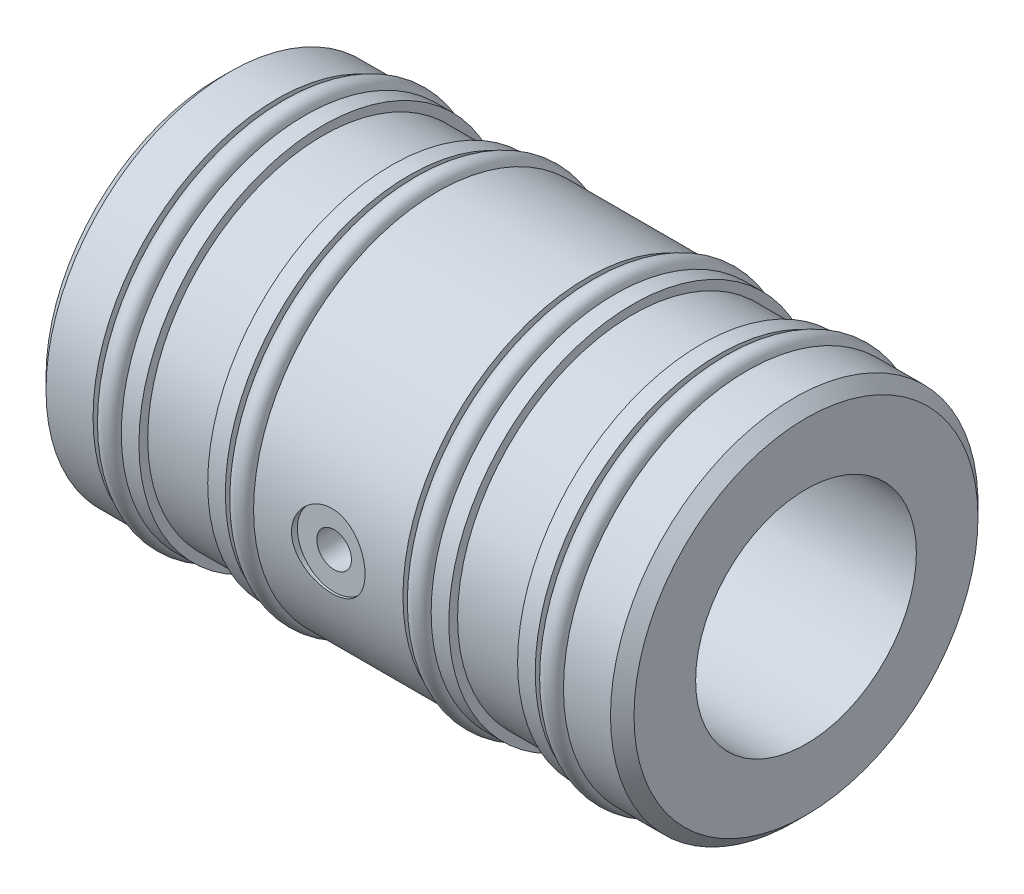
SolidWorks part; units mm, degrees
ref_plane "Front Plane" through (0, 0, 0) normal (0, 0, 1) x (1, 0, 0)
ref_plane "Top Plane" through (0, 0, 0) normal (0, 1, 0) x (1, 0, 0)
ref_plane "Right Plane" through (0, 0, 0) normal (1, 0, 0) x (0, 0, -1)
sketch "Sketch1" plane through (0, 0, 0) normal (0, 0, 1) x (1, 0, 0)
  line L0 (0, 9.5352) -> (50.8, 9.5352)
  line L1 (50.8, 9.5352) -> (50.8, 15.875)
  line L2 (50.8, 15.875) -> (45.72, 15.875)
  line L3 (45.72, 15.875) -> (45.72, 14.605)
  line L4 (45.72, 14.605) -> (43.2816, 14.605)
  line L5 (43.2816, 14.605) -> (43.2816, 15.875)
  line L6 (43.2816, 15.875) -> (41.7576, 15.875)
  line L7 (41.7576, 15.875) -> (41.7576, 15.113)
  line L8 (0, 9.5352) -> (0, 15.875)
  line L9 (0, 15.875) -> (5.08, 15.875)
  line L10 (5.08, 15.875) -> (5.08, 14.605)
  line L11 (5.08, 14.605) -> (7.5184, 14.605)
  line L12 (7.5184, 14.605) -> (7.5184, 15.875)
  line L13 (7.5184, 15.875) -> (9.0424, 15.875)
  line L14 (9.0424, 15.875) -> (9.0424, 15.113)
  line L15 (9.0424, 15.113) -> (14.986, 15.113)
  line L16 (14.986, 15.113) -> (14.986, 15.875)
  line L17 (14.986, 15.875) -> (16.51, 15.875)
  line L18 (16.51, 15.875) -> (16.51, 14.605)
  line L19 (16.51, 14.605) -> (18.9484, 14.605)
  line L20 (18.9484, 14.605) -> (18.9484, 15.875)
  line L21 (18.9484, 15.875) -> (31.8516, 15.875)
  line L22 (31.8516, 15.875) -> (31.8516, 14.605)
  line L23 (41.7576, 15.113) -> (35.814, 15.113)
  line L24 (35.814, 15.113) -> (35.814, 15.875)
  line L25 (35.814, 15.875) -> (34.29, 15.875)
  line L26 (34.29, 15.875) -> (34.29, 14.605)
  line L27 (34.29, 14.605) -> (31.8516, 14.605)
  line L28 (0, 0) -> (50.8, 0) construction
  dimension "Bore ID" = 19.0703
  dimension "OAL" = 50.8
  dimension "Moglice groove width" = 5.9436
  dimension "O-ring groove width" = 2.4384
  dimension "Edge to 1st o-ring groove" = 5.08
  dimension "Edge to 2nd o-ring groove" = 16.51
  dimension "Bushing OD" = 31.75
  dimension "O-ring groove dia" = 29.21
  dimension "Edge to 3rd o-ring groove" = 31.8516
  dimension "edge to 4th o-ring groove" = 43.2816
  dimension "Edge to 1st moglice groove" = 9.0424
  dimension "Edge to 2nd moglice groove" = 35.814
  dimension "Moglice Groove Dia" = 30.226
revolve "Revolve1" add sketch "Sketch1" angle 360 about L28
chamfer "Chamfer1" distance 1.016 angle 45 2 edges at (0, 0, 15.875) (50.8, 0, 15.875)
ref_plane "Plane1" through (0, 0, -7.9121) normal (0, 0, 1) x (1, 0, 0)
hole_wizard "1/4 (0.25) Diameter Hole1" positions "3DSketch1" profile "Sketch2" hole size "1/4" standard "Ansi Inch"
sketch3d "3DSketch1"
  point P0 (25.4, 0, 15.875)
  dimension "Edge to air hole" = 25.4
sketch "Sketch2" plane through (25.4, 0, 15.875) normal (1, 0, 0) x (0, -1, 0)
  line L0 (0, 0) -> (0, 0.508)
  line L1 (0, 0.508) -> (3.175, 0.508)
  line L2 (3.175, 0.508) -> (3.175, 0)
  line L5 (3.175, 0) -> (0, 0)
  line L10 (0, 0.508) -> (-3.175, 0.508) construction
  line L11 (0, -6.35) -> (0, 107.95) construction
  dimension "Hole Dia." = 6.35
  dimension "Hole Depth" = 0.508
  dimension "Drill Angle" = 180
hole_wizard "Air Hole" positions "Sketch4" profile "Sketch3" tap size "M3x0.5" standard "Ansi Metric"
sketch "Sketch4" plane through (0, 0, 15.367) normal (0, 0, 1) x (1, 0, 0)
  circle A0 centre (25.4, 0) radius 3.175 construction
  point P0 (25.4, 0)
sketch "Sketch3" plane through (25.4, 0, 15.367) normal (1, 0, 0) x (0, -1, 0)
  line L0 (0, 0) -> (0, 7.0978)
  line L1 (0, 7.0978) -> (1.2446, 6.35)
  line L2 (1.2446, 6.35) -> (1.2446, 5.9944)
  line L3 (1.2446, 5.9944) -> (1.4986, 5.9944)
  line L4 (1.4986, 5.9944) -> (1.4986, 0)
  line L5 (1.4986, 0) -> (0, 0)
  line L10 (0, 7.0978) -> (-1.2446, 6.35) construction
  line L11 (0, -6.35) -> (0, 107.95) construction
  dimension "Tap Drill Dia." = 2.4892
  dimension "Tap Drill Depth" = 6.35
  dimension "Thread Major Dia." = 2.9972
  dimension "Thread Depth" = 5.9944
  dimension "Drill Angle" = 118
sketch "Sketch5" plane through (0, 0, 0) normal (0, 0, 1) x (1, 0, 0)
  line L0 (0, 0) -> (50.8, 0) construction
  line L1 (5.08, 15.875) -> (5.08, 14.605) construction
  line L2 (16.51, 15.875) -> (16.51, 14.605) construction
  line L3 (31.8516, 15.875) -> (31.8516, 14.605) construction
  line L4 (43.2816, 14.605) -> (43.2816, 15.875) construction
  circle A0 centre (6.2992, 15.4775) radius 0.875
  circle A1 centre (17.7292, 15.4775) radius 0.875
  circle A2 centre (33.0708, 15.4775) radius 0.875
  circle A3 centre (44.5008, 15.4775) radius 0.875
  dimension "D1" = 1.7501
  dimension "D2" = 16.3525
  dimension "D3" = 1.2192
  dimension "D4" = 1.2192
  dimension "D5" = 1.2192
  dimension "D6" = 1.2192
revolve "Revolve2" add sketch "Sketch5" angle 360 about L28
equation "\"plane offset\"= \"Bushing OD@Sketch1\" / 2"
